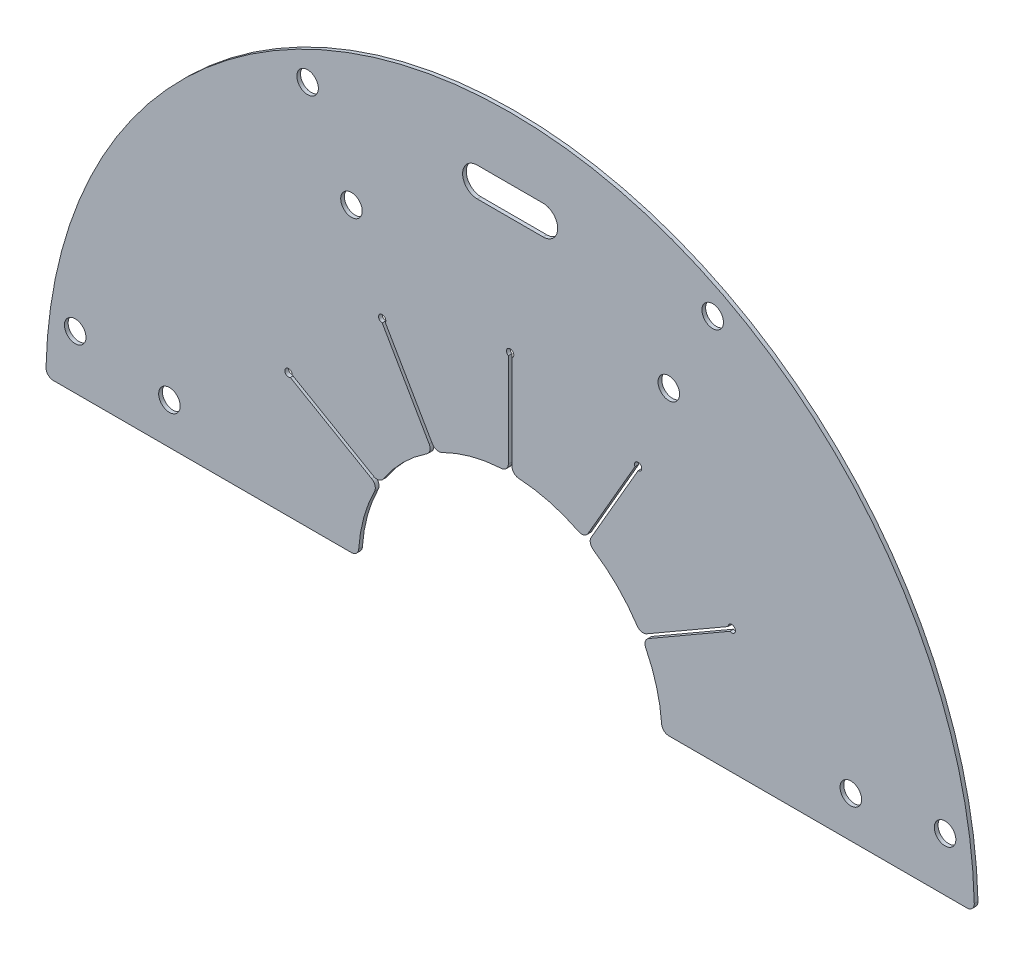
SolidWorks part; units mm, degrees
material "kapton needs fixing aluminized"
ref_plane "Front Plane" through (0, 0, 0) normal (0, 0, 1) x (1, 0, 0)
ref_plane "Top Plane" through (0, 0, 0) normal (0, 1, 0) x (1, 0, 0)
ref_plane "Right Plane" through (0, 0, 0) normal (1, 0, 0) x (0, 0, -1)
sketch "Sketch1" plane through (0, 0, 0) normal (0, 0, 1) x (1, 0, 0)
  line L2 (63.498, 0.5) -> (20.7585, 0.5)
  line L3 (-20.7585, 0.5) -> (-63.498, 0.5)
  arc A0 (63.498, 0.5) -> (-63.498, 0.5) centre (0, 0) ccw
  arc A1 (20.7585, 0.5) -> (-20.7585, 0.5) centre (0, 0) ccw
  dimension "D1" = 63.5
  dimension "D2" = 20.7645
  dimension "D3" = 0.5
extrude "Boss-Extrude1" add sketch "Sketch1" along normal blind 0.508
sketch "Sketch2" plane through (0, 0, 0) normal (0, 0, -1) x (-1, 0, 0)
  line L0 (0, 0) -> (85.0247, 49.089) construction
  line L2 (29.8109, 17.5) -> (17.8563, 10.598)
  line L3 (30.0609, 17.067) -> (18.1063, 10.165)
  line L4 (17.8563, 10.598) -> (18.1063, 10.165)
  line L5 (0, 0) -> (32.2578, 0) construction
  arc A0 (30.0609, 17.067) -> (29.8109, 17.5) centre (30.3109, 17.5) ccw
  circle A1 centre (0, 0) radius 35 construction
  arc A2 (20.7585, 0.5) -> (-20.7585, 0.5) centre (0, 0) ccw construction
  dimension "D2" = 70
  dimension "D3" = 1
  dimension "D1" = 30
  dimension "D4" = 0.5
extrude "Cut-Extrude1" cut sketch "Sketch2" against normal through all
pattern_circular "CirPattern1" count 5 every 30 about axis through (0, 0, 0) along (0, 0, 1) of "Cut-Extrude1"
fillet "Fillet1" radius 1 14 edges at (63.498, 0.5, 0.254) (20.7585, 0.5, 0.254) (-63.498, 0.5, 0.254) (-20.7585, 0.5, 0.254)
hole_wizard "#4 Clearance Hole1" positions "Sketch4" profile "Sketch3" hole size "#4" standard "ANSI Inch"
sketch "Sketch4" plane through (0, 0, 0) normal (0, 0, -1) x (-1, 0, 0)
  line L0 (0, 0) -> (-18.6296, 0) construction
  line L1 (0, 0) -> (-16.6638, 2.1938) construction
  point P0 (-59.4867, 7.8316)
  point P8 (-46.5979, 6.1347)
  dimension "D1" = 7.5
  dimension "D2" = 60
  dimension "D3" = 47
sketch "Sketch3" plane through (59.4867, 7.8316, 0) normal (1, 0, 0) x (0, 1, 0)
  line L0 (0, 0) -> (0, 136.7752)
  line L1 (0, 136.7752) -> (1.4732, 135.89)
  line L2 (1.4732, 135.89) -> (1.4732, 0)
  line L5 (1.4732, 0) -> (0, 0)
  line L10 (0, 136.7752) -> (-1.4732, 135.89) construction
  line L11 (0, -6.35) -> (0, 107.95) construction
  dimension "Hole Dia." = 2.9464
  dimension "Hole Depth" = 135.89
  dimension "Drill Angle" = 118
pattern_circular "CirPattern2" count 4 every 55 about axis through (0, 0, 0) along (0, 0, 1) of "#4 Clearance Hole1"
sketch "Sketch5" plane through (0, 0, 0) normal (0, 0, -1) x (-1, 0, 0)
  line L0 (-4.5, 53) -> (4.5, 53) construction
  line L1 (-4.5, 55) -> (4.5, 55)
  line L2 (-4.5, 51) -> (4.5, 51)
  line L3 (0, 0) -> (12.5102, 0) construction
  line L4 (0, 0) -> (0, 15.43) construction
  arc A0 (-4.5, 55) -> (-4.5, 51) centre (-4.5, 53) ccw
  arc A1 (4.5, 51) -> (4.5, 55) centre (4.5, 53) ccw
  point P2 (0, 53)
  dimension "D1" = 53
  dimension "D2" = 4
  dimension "D3" = 9
extrude "Cut-Extrude2" cut sketch "Sketch5" against normal through all
